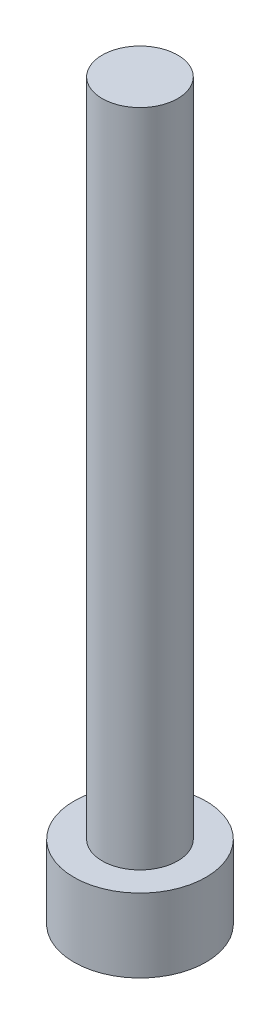
SolidWorks part; units mm, degrees
ref_plane "前视基准面" through (0, 0, 0) normal (0, 0, 1) x (1, 0, 0)
ref_plane "上视基准面" through (0, 0, 0) normal (0, 1, 0) x (1, 0, 0)
ref_plane "右视基准面" through (0, 0, 0) normal (1, 0, 0) x (0, 0, -1)
sketch "草图1" plane through (0, 0, 0) normal (0, 1, 0) x (1, 0, 0)
  circle A0 centre (0, 0) radius 3.5
extrude "凸台-拉伸1" add sketch "草图1" along normal blind 3.9
sketch "草图2" plane through (0, 3.9, 0) normal (0, 1, 0) x (1, 0, 0)
  circle A0 centre (0, 0) radius 2
extrude "凸台-拉伸2" add sketch "草图2" along normal blind 35
sketch "草图3" plane through (0, 0, 0) normal (0, -1, 0) x (1, 0, 0)
  line L1 (1.725, 0) -> (0.8625, 1.4939)
  line L2 (0.8625, 1.4939) -> (-0.8625, 1.4939)
  line L3 (-0.8625, 1.4939) -> (-1.725, 0)
  line L4 (-1.725, 0) -> (-0.8625, -1.4939)
  line L5 (-0.8625, -1.4939) -> (0.8625, -1.4939)
  line L6 (0.8625, -1.4939) -> (1.725, 0)
  circle A0 centre (0, 0) radius 1.4939 construction
extrude "切除-拉伸1" cut sketch "草图3" against normal blind 2.4
